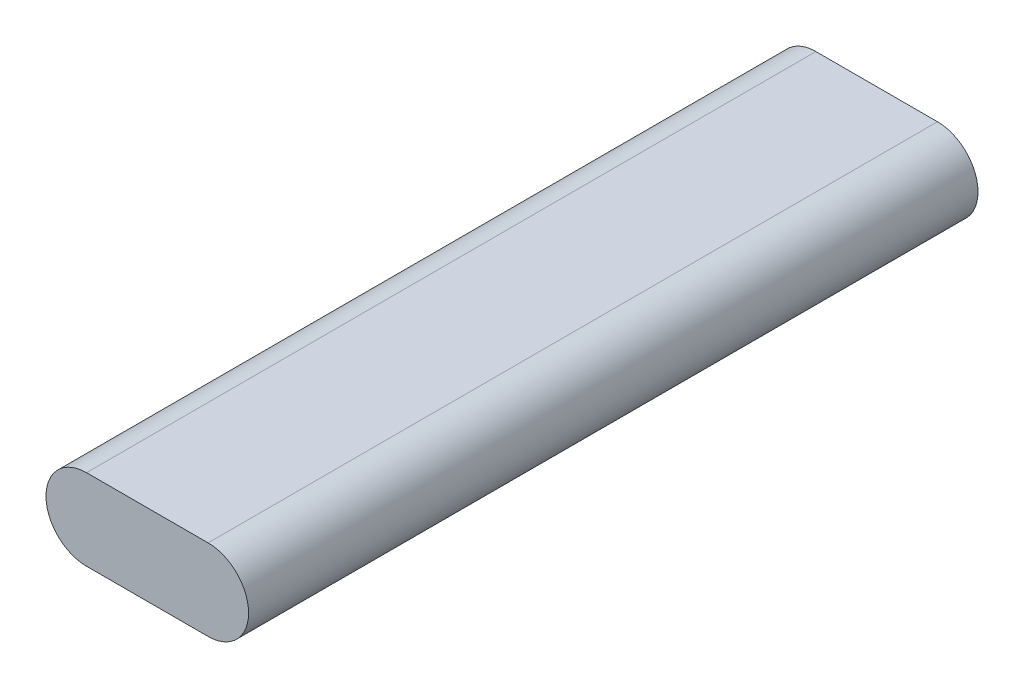
SolidWorks part; units mm, degrees
ref_plane "Plano frontal" through (0, 0, 0) normal (0, 0, 1) x (1, 0, 0)
ref_plane "Plano superior" through (0, 0, 0) normal (0, 1, 0) x (1, 0, 0)
ref_plane "Plano direito" through (0, 0, 0) normal (1, 0, 0) x (0, 0, -1)
sketch "Esboço1" plane through (0, 0, 0) normal (0, 0, 1) x (1, 0, 0)
  line L0 (-7.5, 0) -> (7.5, 0) construction
  line L1 (-7.5, 5) -> (7.5, 5)
  line L2 (-7.5, -5) -> (7.5, -5)
  line L3 (-7.5, 0) -> (-12.5, 0) construction
  line L4 (7.5, 0) -> (12.5, 0) construction
  arc A0 (-7.5, 5) -> (-7.5, -5) centre (-7.5, 0) ccw
  arc A1 (7.5, -5) -> (7.5, 5) centre (7.5, 0) ccw
  point P2 (0, 0)
  point P11 (0, 0)
  dimension "D1" = 10
  dimension "25" = 25
extrude "Ressalto-extrusão1" add sketch "Esboço1" along normal mid plane 90
